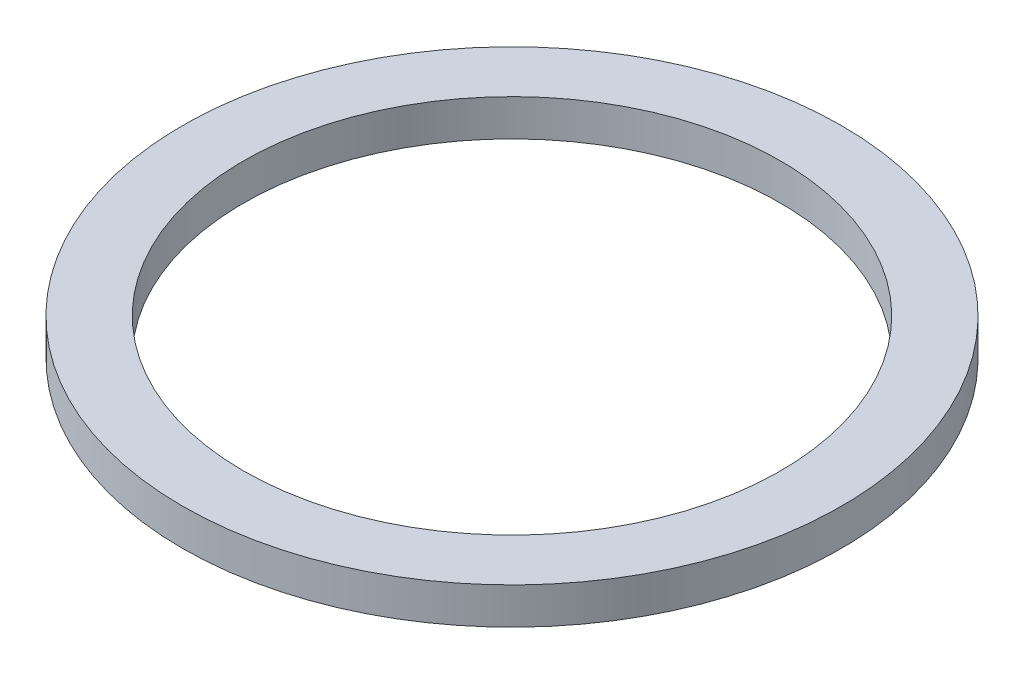
SolidWorks part; units mm, degrees
ref_plane "Front Plane" through (0, 0, 0) normal (0, 0, 1) x (1, 0, 0)
ref_plane "Top Plane" through (0, 0, 0) normal (0, 1, 0) x (1, 0, 0)
ref_plane "Right Plane" through (0, 0, 0) normal (1, 0, 0) x (0, 0, -1)
sketch "Sketch1" plane through (0, 0, 0) normal (0, 1, 0) x (1, 0, 0)
  circle A0 centre (0, 0) radius 22
  circle A1 centre (0, 0) radius 27
  dimension "D1" = 5
  dimension "D2" = 54
extrude "Boss-Extrude1" add sketch "Sketch1" along normal blind 3
